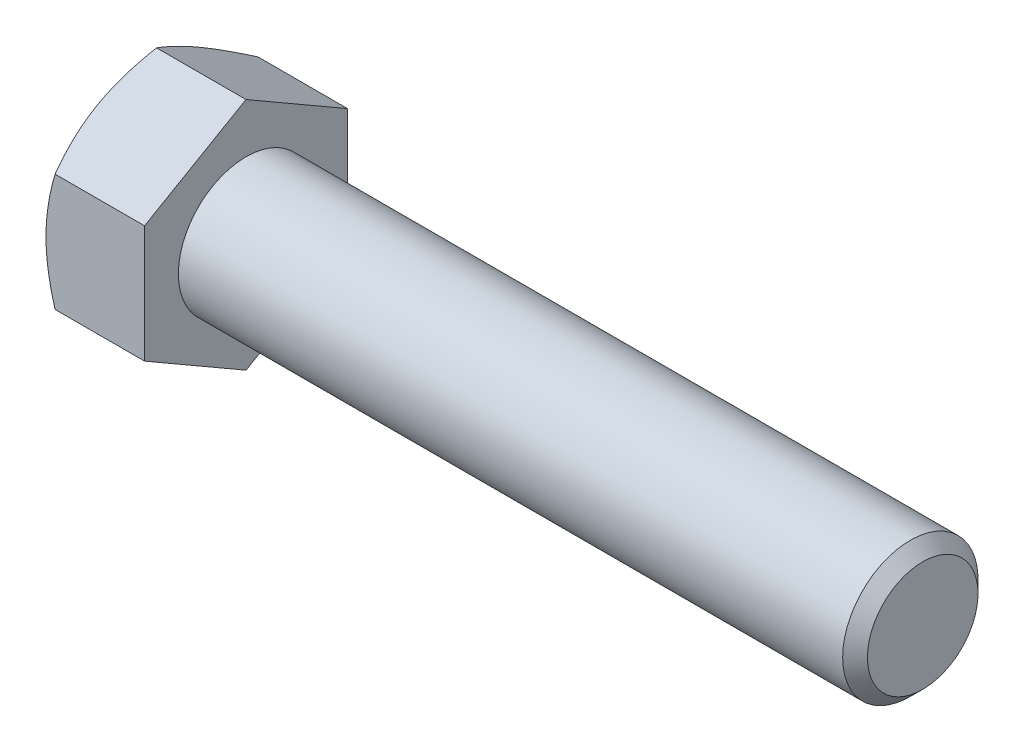
SolidWorks part; units mm, degrees
extrude "BaseHead" add sketch "Sketch1" along normal blind 9.2456
sketch "Sketch1" plane through (0, 0, 0) normal (1, 0, 0) x (0, 0, -1)
  line L0 (9.525, 5.4993) -> (9.525, -5.4993)
  line L1 (-9.525, 5.4993) -> (-9.525, -5.4993)
  line L2 (9.525, -5.4993) -> (0, -10.9985)
  line L3 (0, -10.9985) -> (-9.525, -5.4993)
  line L4 (9.525, 5.4993) -> (0, 10.9985)
  line L5 (0, 10.9985) -> (-9.525, 5.4993)
  dimension "Width_flats" = 19.05
  dimension "D2" = 120
  dimension "D3" = 9.525
  dimension "D4" = 9.525
  dimension "D5" = 9.525
ref_plane "Plane1" through (0, 0, 0) normal (0, 0, 1) x (1, 0, 0)
ref_plane "Plane2" through (0, 0, 0) normal (0, 1, 0) x (1, 0, 0)
ref_plane "Plane3" through (0, 0, 0) normal (1, 0, 0) x (0, 0, -1)
other "Configuration Table"
sketch "BodySke" plane through (0, 0, 0) normal (0, 0, 1) x (1, 0, 0)
  line L0 (0, 5.4993) -> (0, -5.4993) construction
  line L1 (0, 0) -> (72.7456, 0)
  line L2 (0, 0) -> (0, 6.35)
  line L3 (0, 6.35) -> (71.5823, 6.35)
  line L4 (72.7456, 0) -> (72.7456, 5.1867)
  line L5 (9.2456, 10.9985) -> (9.2456, 5.4993) construction
  line L6 (72.7456, 5.1867) -> (71.5823, 6.35)
  line L7 (0, 0) -> (96.52, 0) construction
  line L8 (72.7456, -5.1867) -> (71.5823, -6.35) construction
  line L9 (0, -6.35) -> (71.5823, -6.35) construction
  line L10 (11.1989, 15.24) -> (11.1989, -2.54) construction
  line L11 (40.9956, 15.24) -> (40.9956, -2.54) construction
  line L12 (9.2456, 5.4993) -> (9.2456, -5.4993) construction
  dimension "Diameter" = 12.7
revolve "BaseBody" add sketch "BodySke" angle 360 about L7
cosmetic thread "ThreadCosmetic" [suppressed] parameters "Thread_length"=31.75, "Thread_minor"=10.3734
sketch "Sketch3" plane through (0, 0, 0) normal (0, 0, 1) x (1, 0, 0)
  line L0 (0, 9.525) -> (4.5169, 17.3485)
  line L1 (0, 10.9985) -> (0, 5.4993) construction
  line L2 (4.5169, 17.3485) -> (4.5169, 23.6985)
  line L3 (4.5169, 23.6985) -> (-12.7, 23.6985)
  line L4 (-12.7, 23.6985) -> (-12.7, 9.525)
  line L5 (-12.7, 9.525) -> (0, 9.525)
  line L6 (0, 0) -> (99.06, 0) construction
  line L7 (9.2456, 10.9985) -> (0, 10.9985) construction
  dimension "D1" = 9.525
  dimension "D2" = 6.35
  dimension "D3" = 12.7
  dimension "D4" = 6.35
  dimension "Head_ch_ang" = 30
revolve "HeadChamfer" cut sketch "Sketch3" angle 360 about L6
fillet "HeadFillet" [suppressed] radius 0.762
sketch "ThdSchSke" plane through (0, 0, 0) normal (0, 0, 1) x (1, 0, 0)
  line L0 (40.9956, -5.1867) -> (40.181, -6.35)
  line L1 (40.9956, -5.1867) -> (41.8102, -6.35)
  line L2 (41.8102, -6.35) -> (41.8102, -7.9375)
  line L3 (-3.175, 0) -> (5.1513, 0) construction
  line L5 (41.8102, -7.9375) -> (40.181, -7.9375)
  line L6 (40.181, -7.9375) -> (40.181, -6.35)
  dimension "Thread_minor" = 10.3734
  dimension "Diameter" = 12.7
  dimension "Start" = 40.9956
revolve "ThreadSchematic" [suppressed] cut sketch "ThdSchSke" angle 360 about L3
pattern_linear "ThdSchPat" [suppressed]
equation "\"D3@Sketch1\" = \"Width_flats@Sketch1\" / 2"
equation "\"D4@Sketch1\" = \"D3@Sketch1\""
equation "\"D5@Sketch1\" = \"D4@Sketch1\""
equation "\"Thread_minor@ThreadCosmetic\" = \"Minor_dia@BodySke\""
equation "\"D1@Sketch3\" = \"Width_flats@Sketch1\" / 2"
equation "\"Thread_length@ThreadCosmetic\" = ((sgn( (\"Length@BodySke\" - \"Advance@BodySke\" ) - \"Thread_nom@BodySke\" )-1)*( (\"Length@BodySke\" - \"Advance@BodySke\" ) - \"Thread_nom@BodySke\" ))/-2+ \"Thread_nom@BodySke\""
equation "\"Thread_minor@ThdSchSke\" = \"Minor_dia@BodySke\""
equation "\"Diameter@ThdSchSke\" = \"Diameter@BodySke\""
equation "\"Overcut@ThdSchSke\" = \"Diameter@BodySke\" * 1.25"
equation "\"Start@ThdSchSke\" = \"Head_ht@BaseHead\" + \"Length@BodySke\" - \"Thread_length@ThreadCosmetic\"  '---Non-countersunk---"
equation "\"Num_threads@ThdSchPat\" = int( \"Thread_length@ThreadCosmetic\" / \"Advance@BodySke\" + 0.999 )  + 1"
equation "\"Advance@ThdSchPat\" = \"Thread_length@ThreadCosmetic\" /  (\"Num_threads@ThdSchPat\" - 1) 'relax it"
equation "\"Num_threads@ThdSchPat\" = \"Num_threads@ThdSchPat\" - sgn( \"Num_threads@ThdSchPat\" - 1) '---chamfered tips only---"
